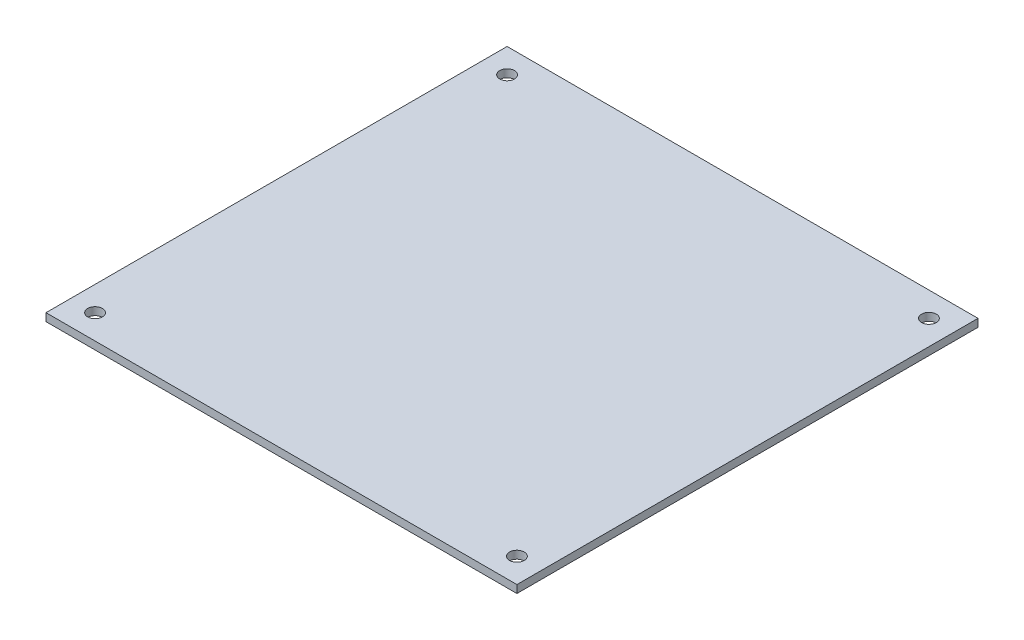
SolidWorks part; units mm, degrees
material "FR-4"
ref_plane "Front Plane" through (0, 0, 0) normal (0, 0, 1) x (1, 0, 0)
ref_plane "Top Plane" through (0, 0, 0) normal (0, 1, 0) x (1, 0, 0)
ref_plane "Right Plane" through (0, 0, 0) normal (1, 0, 0) x (0, 0, -1)
sketch "Sketch1" plane through (0, 0, 0) normal (0, 1, 0) x (1, 0, 0)
  line L1 (-48, -47) -> (48, -47)
  line L2 (-48, -47) -> (-48, 47)
  line L3 (-48, 47) -> (48, 47)
  line L4 (48, -47) -> (48, 47)
  line L5 (-48, -47) -> (48, 47) construction
  line L6 (-48, 47) -> (48, -47) construction
  point P0 (0, 0)
  dimension "D1" = 96
  dimension "D2" = 94
extrude "Boss-Extrude1" add sketch "Sketch1" along normal blind 1.5875 contours L2 L3 L4 L1
sketch "Sketch2" plane through (0, 1.5875, 0) normal (0, 1, 0) x (1, 0, 0)
  line L8 (-43, -42) -> (43, -42)
  line L9 (43, -42) -> (43, 42)
  line L10 (43, 42) -> (-43, 42)
  line L11 (-43, 42) -> (-43, -42)
  line L12 (-43, -42) -> (43, -42) construction
  line L13 (43, -42) -> (43, 42) construction
  line L14 (43, 42) -> (-43, 42) construction
  line L15 (-43, 42) -> (-43, -42) construction
  circle A0 centre (-43, 42) radius 1.5
  circle A1 centre (43, 42) radius 1.5
  circle A2 centre (43, -42) radius 1.5
  circle A3 centre (-43, -42) radius 1.5
  dimension "D2" = 3
  dimension "D1" = 5
extrude "Cut-Extrude1" cut sketch "Sketch2" against normal through all
